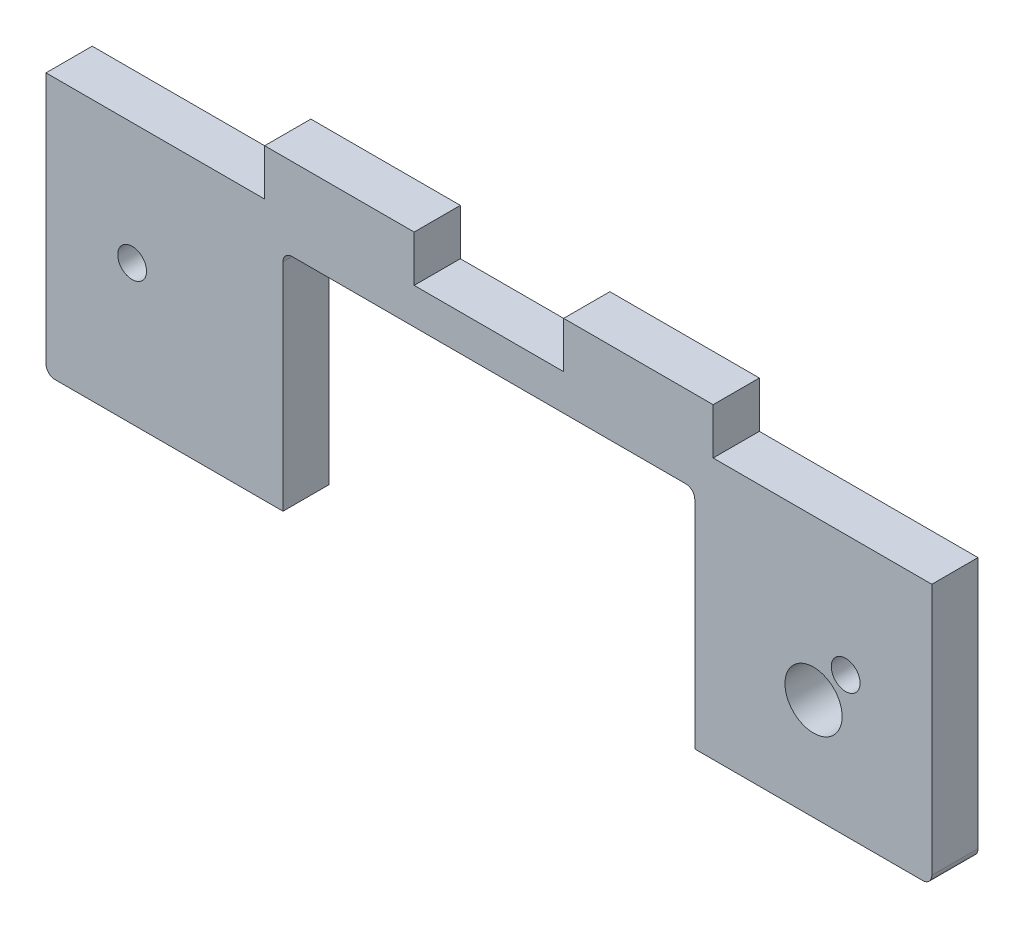
SolidWorks part; units mm, degrees
ref_plane "Front Plane" through (0, 0, 0) normal (0, 0, 1) x (1, 0, 0)
ref_plane "Top Plane" through (0, 0, 0) normal (0, 1, 0) x (1, 0, 0)
ref_plane "Right Plane" through (0, 0, 0) normal (1, 0, 0) x (0, 0, -1)
sketch "Sketch1" plane through (0, 0, 0) normal (0, 0, 1) x (1, 0, 0)
  line L1 (-56.4888, 30.3567) -> (41.8712, 30.3567)
  line L2 (-56.4888, 30.3567) -> (-56.4888, 2.3567)
  line L3 (-55.4888, 1.3567) -> (40.8712, 1.3567)
  line L4 (41.8712, 30.3567) -> (41.8712, 2.3567)
  arc A0 (40.8712, 1.3567) -> (41.8712, 2.3567) centre (40.8712, 2.3567) ccw
  arc A1 (-55.4888, 1.3567) -> (-56.4888, 2.3567) centre (-55.4888, 2.3567) cw
  point P6 (41.8712, 1.3567)
  dimension "D3" = 1
  dimension "D1" = 98.36
  dimension "D2" = 29
extrude "Main" add sketch "Sketch1" along normal blind 5.13
sketch "Sketch2" plane through (0, 30.3567, 0) normal (0, 1, 0) x (1, 0, 0)
  line L0 (41.8712, -5.13) -> (-56.4888, -5.13) construction
  line L1 (0.9912, -5.13) -> (17.5912, -5.13)
  line L2 (0.9912, -5.13) -> (0.9912, 0)
  line L3 (0.9912, 0) -> (17.5912, 0)
  line L4 (17.5912, -5.13) -> (17.5912, 0)
  line L5 (41.8712, 0) -> (-56.4888, 0) construction
  line L6 (-32.2088, -5.13) -> (-15.6088, -5.13)
  line L7 (-32.2088, -5.13) -> (-32.2088, 0)
  line L8 (-32.2088, 0) -> (-15.6088, 0)
  line L9 (-15.6088, -5.13) -> (-15.6088, 0)
  line L10 (41.8712, -5.13) -> (41.8712, 0) construction
  dimension "D1" = 16.6
  dimension "D3" = 49.8
  dimension "D4" = 24.28
  dimension "D2" = 2
extrude "Teeth" add sketch "Sketch2" along normal blind 5.13
hole_wizard "M3 Clearance Hole1" positions "Sketch4" profile "Sketch3" hole size "M3" standard "Ansi Metric" end condition up to next
sketch "Sketch4" plane through (0, 0, 5.13) normal (0, 0, 1) x (1, 0, 0)
  line L0 (-56.4888, 30.3567) -> (-56.4888, 2.3567) construction
  line L1 (-55.4888, 1.3567) -> (40.8712, 1.3567) construction
  line L2 (41.8712, 2.3567) -> (41.8712, 30.3567) construction
  point P0 (-46.9238, 16.8567)
  point P1 (32.3062, 16.8567)
  dimension "D1" = 9.565
  dimension "D2" = 15.5
  dimension "D3" = 9.565
  dimension "D4" = 15.5
sketch "Sketch3" plane through (-46.9238, 16.8567, 5.13) normal (1, 0, 0) x (0, -1, 0)
  line L0 (0, 0) -> (0, 5.13)
  line L1 (0, 5.13) -> (1.6, 5.13)
  line L2 (1.6, 5.13) -> (1.6, 0)
  line L5 (1.6, 0) -> (0, 0)
  line L11 (0, -6.35) -> (0, 107.95) construction
  dimension "Thru Hole Dia." = 3.2
  dimension "Thru Hole Depth" = 5.13
sketch "Sketch5" plane through (0, 0, 5.13) normal (0, 0, 1) x (1, 0, 0)
  line L0 (-55.4888, 1.3567) -> (40.8712, 1.3567) construction
  line L1 (-29.1688, 26.3567) -> (14.5512, 26.3567)
  line L2 (-30.1688, 25.3567) -> (-30.1688, 1.3567)
  line L3 (-30.1688, 1.3567) -> (15.5512, 1.3567)
  line L4 (15.5512, 25.3567) -> (15.5512, 1.3567)
  line L5 (41.8712, 2.3567) -> (41.8712, 30.3567) construction
  arc A0 (15.5512, 25.3567) -> (14.5512, 26.3567) centre (14.5512, 25.3567) ccw
  arc A1 (-30.1688, 25.3567) -> (-29.1688, 26.3567) centre (-29.1688, 25.3567) cw
  point P10 (15.5512, 26.3567)
  point P13 (-30.1688, 26.3567)
  dimension "D4" = 1
  dimension "D1" = 45.72
  dimension "D2" = 25
  dimension "D3" = 26.32
extrude "Hinge slot" cut sketch "Sketch5" against normal up to next
sketch "Sketch6" plane through (0, 0, 5.13) normal (0, 0, 1) x (1, 0, 0)
  line L1 (41.8712, 2.3567) -> (41.8712, 30.3567) construction
  circle A0 centre (28.7382, 12.6521) radius 3.175
  dimension "D1" = 6.35
  dimension "D2" = 13.133
extrude "Thermistor wires hole" cut sketch "Sketch6" against normal up to next
equation "\"D4@Sketch2\" = (\"D1@Sketch1\"-\"D3@Sketch2\")/2"
equation "\"D3@Sketch4\" = \"D1@Sketch4\""
equation "\"D4@Sketch4\" = \"D2@Sketch4\""
equation "\"D3@Sketch5\" = (\"D1@Sketch1\"-\"D1@Sketch5\")/2"
